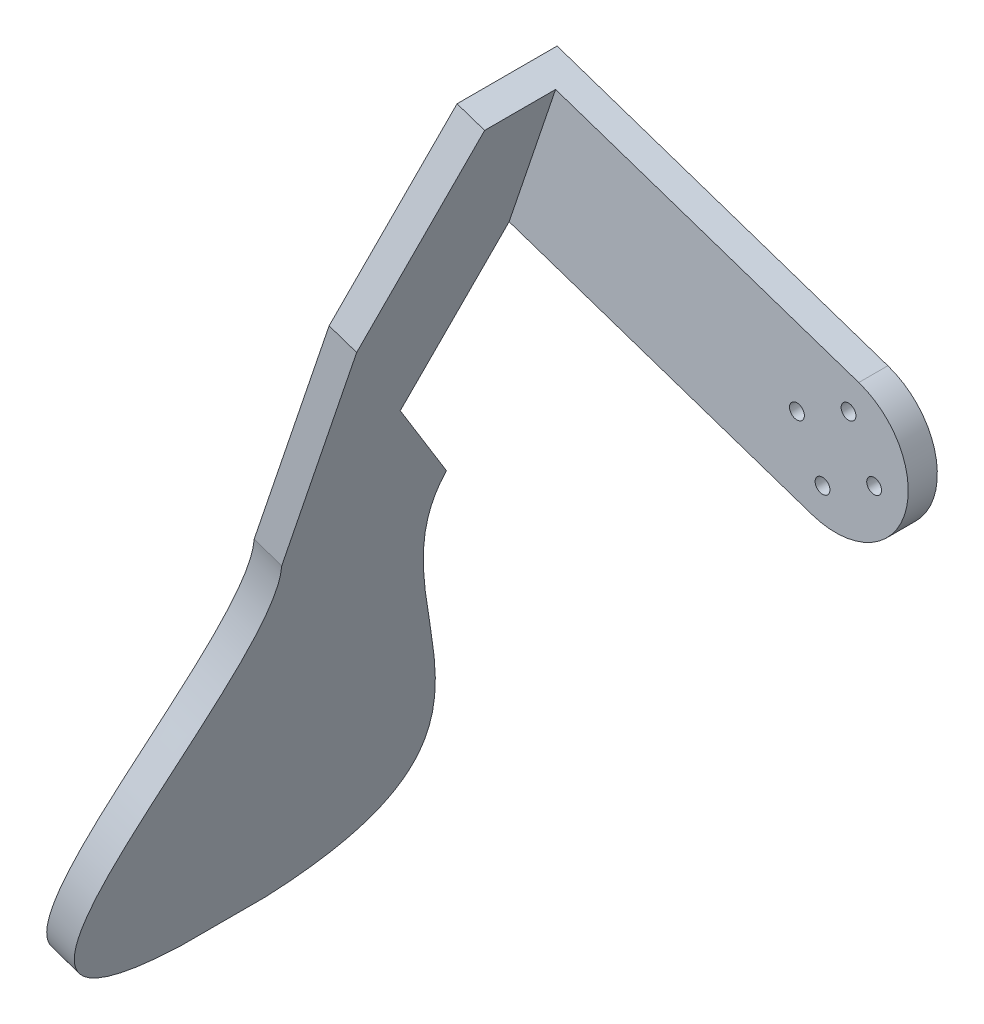
SolidWorks part; units mm, degrees
ref_plane "Front Plane" through (0, 0, 0) normal (0, 0, 1) x (1, 0, 0)
ref_plane "Top Plane" through (0, 0, 0) normal (0, 1, 0) x (1, 0, 0)
ref_plane "Right Plane" through (0, 0, 0) normal (1, 0, 0) x (0, 0, -1)
sketch "Sketch2" plane through (0, 0, 0) normal (0, 0, 1) x (1, 0, 0)
  line L0 (9.4757, -3.1954) -> (-9.4757, 3.1954) construction
  line L1 (-218.1857, 80.2001) -> (-122.24, 47.8453) construction
  line L2 (-3.1954, -9.4757) -> (3.1954, 9.4757) construction
  circle A0 centre (0, 0) radius 10
  circle A1 centre (6.633, -2.2368) radius 1.275
  circle A4 centre (-2.2368, -6.633) radius 1.275
  circle A5 centre (0, 0) radius 10 construction
  circle A6 centre (-6.633, 2.2368) radius 1.275
  circle A7 centre (2.2368, 6.633) radius 1.275
  point P21 (0, 0)
  dimension "D1" = 2.55
  dimension "D2" = 2.55
  dimension "D3" = 7
  dimension "D4" = 7
extrude "Boss-Extrude1" add sketch "Sketch2" along normal blind 3
sketch "Sketch3" plane through (0, 0, 3) normal (0, 0, 1) x (1, 0, 0)
  line L0 (11.8447, -3.9943) -> (-11.8447, 3.9943) construction
  line L1 (-3.9943, -11.8447) -> (3.9943, 11.8447) construction
  line L3 (-3.9943, -11.8447) -> (-60.8486, 7.3278)
  line L4 (3.9943, 11.8447) -> (-52.8601, 31.0171)
  line L5 (-60.8486, 7.3278) -> (-52.8601, 31.0171)
  line L6 (-218.1857, 80.2001) -> (-122.24, 47.8453) construction
  arc A0 (-3.9943, -11.8447) -> (3.9943, 11.8447) centre (0, 0) ccw
  circle A1 centre (6.633, -2.2368) radius 1.275
  circle A2 centre (-2.2368, -6.633) radius 1.275
  circle A3 centre (-6.633, 2.2368) radius 1.275
  circle A4 centre (2.2368, 6.633) radius 1.275
  circle A5 centre (0, 0) radius 10 construction
  point P14 (0, 0)
  dimension "D1" = 2.55
  dimension "D2" = 2.55
  dimension "D5" = 25
  dimension "D3" = 7
  dimension "D4" = 7
  dimension "D6" = 60
extrude "Boss-Extrude2" add sketch "Sketch3" against normal blind 5
sketch "Sketch4" plane through (-56.8544, 19.1724, 0) normal (-0.9476, 0.3195, 0) x (0.3195, 0.9476, 0)
  line L2 (-62.9426, -25.9706) -> (-22.6277, -25.9706)
  line L5 (12.5, -3) -> (-12.5, -3)
  line L9 (-62.9426, 2.3494) -> (-42.3963, -12.1672)
  line L10 (12.5, -3) -> (12.5, -15.1993)
  line L11 (23.5514, -11.8106) -> (-140.1922, -11.8106) construction
  line L12 (-139.2081, -4.3106) -> (-139.2081, -19.3106)
  line L13 (12.5, -15.1993) -> (-22.6277, -25.9706)
  line L14 (-12.5, -3) -> (-42.3963, -12.1672)
  line L17 (12.5, 2) -> (12.5, -3) construction
  spline S0 degree 3 poles (-62.9426, 2.3494) (-87.4923, -4.5092) (-135.6025, 45.4263) (-139.2081, -4.3106) knots 0 0 0 0 1 1 1 1
  spline S1 degree 3 poles (-62.9426, -25.9706) (-87.4923, -19.1119) (-135.6025, -69.0474) (-139.2081, -19.3106) knots 0 0 0 0 1 1 1 1
  point P8 (-91.4881, 8.073)
  point P11 (-128.2902, 17.123)
  point P17 (-153.1136, -12.427)
  dimension "D1" = 18.9923
  dimension "D2" = 25.1572
  dimension "D3" = 31.2702
extrude "Boss-Extrude3" add sketch "Sketch4" against normal blind 5
